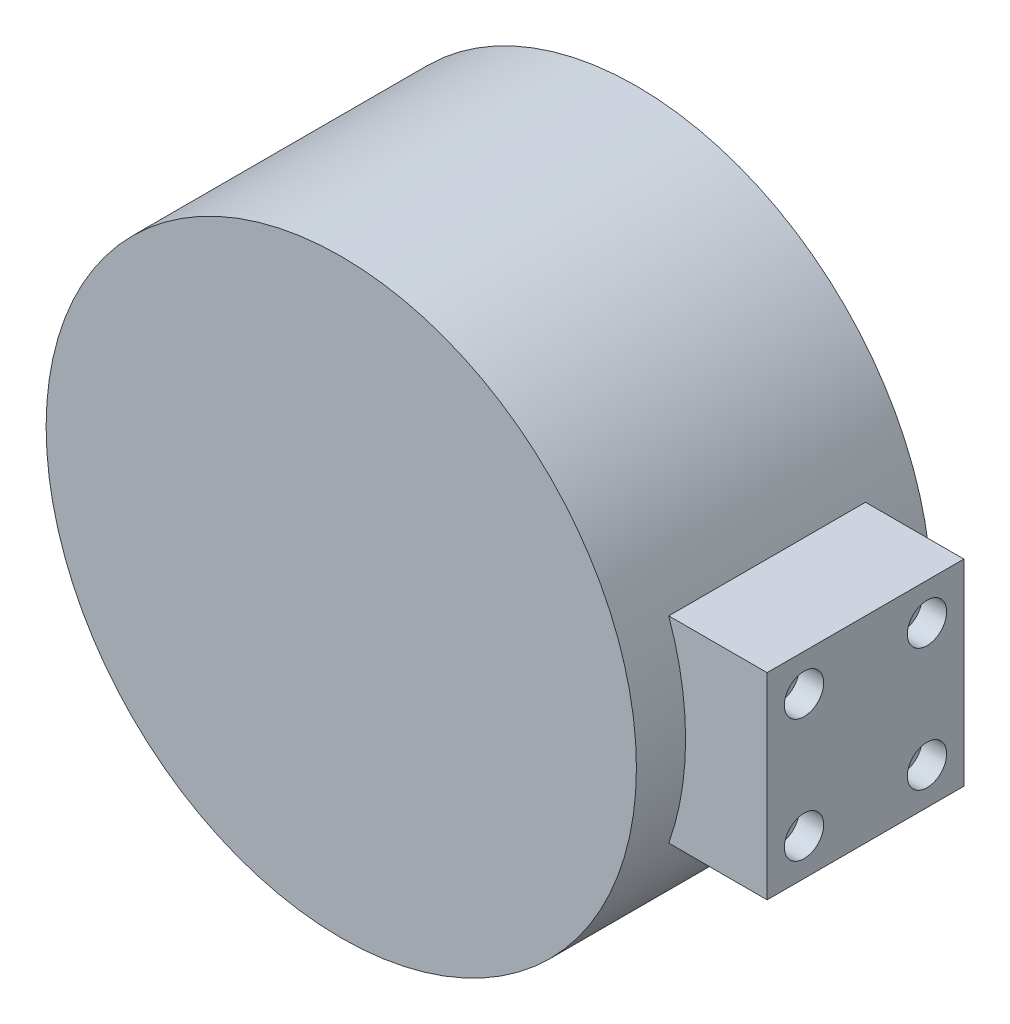
SolidWorks part; units mm, degrees
ref_plane "前视基准面" through (0, 0, 0) normal (0, 0, 1) x (1, 0, 0)
ref_plane "上视基准面" through (0, 0, 0) normal (0, 1, 0) x (1, 0, 0)
ref_plane "右视基准面" through (0, 0, 0) normal (1, 0, 0) x (0, 0, -1)
sketch "草图1" plane through (0, 0, 0) normal (0, 0, 1) x (1, 0, 0)
  line L0 (56.5685, -20) -> (76.5685, -20)
  line L1 (76.5685, -20) -> (76.5685, 20)
  line L2 (76.5685, 20) -> (56.5685, 20)
  line L3 (0, 0) -> (-23.6899, 0) construction
  arc A0 (56.5685, 20) -> (56.5685, -20) centre (0, 0) ccw
  dimension "D1" = 120
  dimension "D2" = 40
  dimension "D3" = 20
extrude "凸台-拉伸1" add sketch "草图1" along normal blind 60
sketch "草图2" plane through (0, 0, 0) normal (0, 0, -1) x (-1, 0, 0)
  line L0 (-76.5685, 20) -> (-76.5685, -20)
  line L1 (-76.5685, -20) -> (-56.5685, -20)
  line L2 (-76.5685, 20) -> (-56.5685, 20)
  arc A0 (-56.5685, 20) -> (-56.5685, -20) centre (0, 0) ccw
extrude "切除-拉伸1" cut sketch "草图2" against normal blind 10
sketch "草图3" plane through (0, 0, 60) normal (0, 0, 1) x (1, 0, 0)
  line L0 (76.5685, 20) -> (76.5685, -20)
  line L1 (76.5685, -20) -> (56.5685, -20)
  line L2 (76.5685, 20) -> (56.5685, 20)
  arc A0 (56.5685, -20) -> (56.5685, 20) centre (0, 0) ccw
extrude "切除-拉伸2" cut sketch "草图3" against normal blind 10
sketch "草图4" plane through (0, 0, 0) normal (0, 0, -1) x (-1, 0, 0)
  circle A0 centre (0, 0) radius 40
  dimension "D1" = 80
extrude "切除-拉伸3" cut sketch "草图4" against normal blind 20
sketch "草图5" plane through (76.5685, 0, 0) normal (1, 0, 0) x (0, 0, -1)
  line L0 (-50, 20) -> (-10, -20) construction
  line L2 (-42.5, 12.5) -> (-17.5, 12.5) construction
  line L3 (-42.5, 12.5) -> (-42.5, -12.5) construction
  line L4 (-42.5, -12.5) -> (-17.5, -12.5) construction
  line L5 (-17.5, 12.5) -> (-17.5, -12.5) construction
  line L6 (-42.5, 12.5) -> (-17.5, -12.5) construction
  line L7 (-42.5, -12.5) -> (-17.5, 12.5) construction
  circle A0 centre (-17.5, 12.5) radius 4
  circle A1 centre (-17.5, -12.5) radius 4
  circle A2 centre (-42.5, -12.5) radius 4
  circle A3 centre (-42.5, 12.5) radius 4
  point P4 (-30, 0)
  dimension "D2" = 8
  dimension "D1" = 25
extrude "切除-拉伸4" cut sketch "草图5" against normal blind 5
